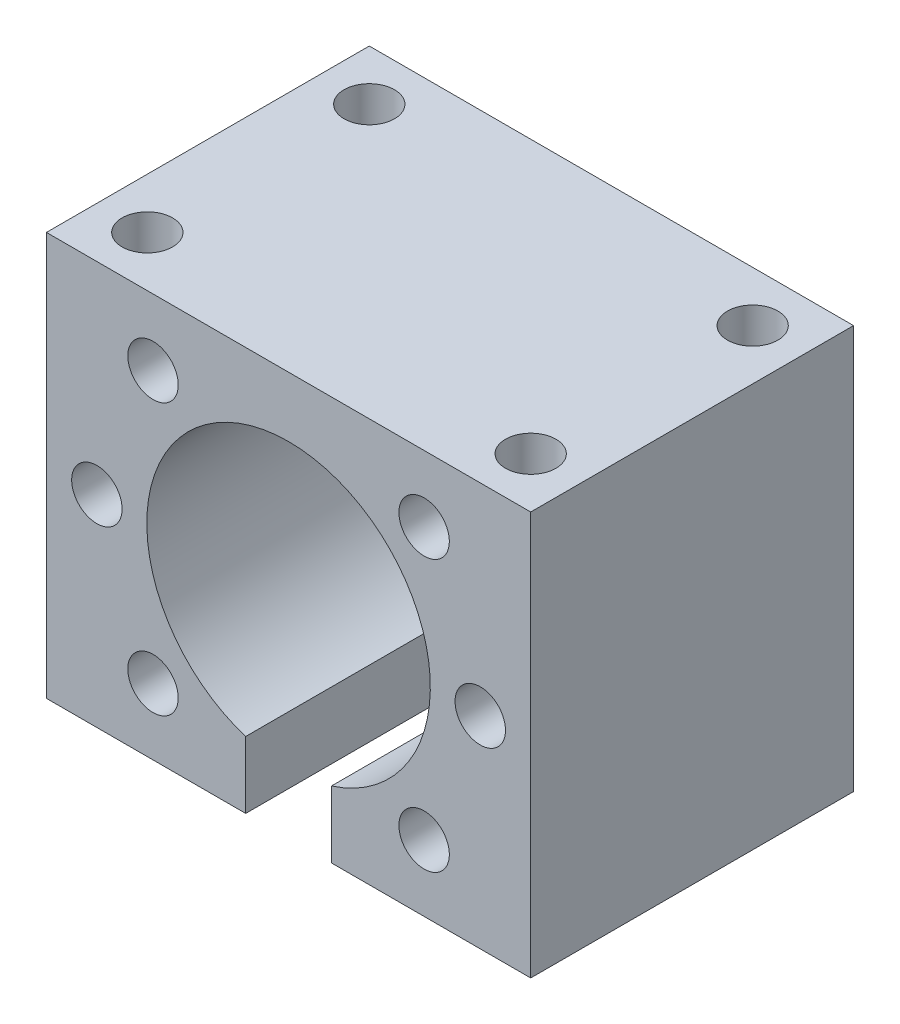
SolidWorks part; units mm, degrees
ref_plane "Front Plane" through (0, 0, 0) normal (0, 0, 1) x (1, 0, 0)
ref_plane "Top Plane" through (0, 0, 0) normal (0, 1, 0) x (1, 0, 0)
ref_plane "Right Plane" through (0, 0, 0) normal (1, 0, 0) x (0, 0, -1)
sketch "Sketch1" plane through (0, 0, 0) normal (0, 0, 1) x (1, 0, 0)
  line L0 (0, 0) -> (0, 43.8498) construction
  line L1 (-24, 40) -> (-24, 0)
  line L2 (-24, 0) -> (-4.25, 0)
  line L3 (-24, 40) -> (24, 40)
  line L4 (0, 20) -> (-28.6191, 20) construction
  line L5 (-4.25, 0) -> (-4.25, 6.6082)
  line L6 (4.25, 0) -> (4.25, 6.6082)
  line L7 (24, 0) -> (4.25, 0)
  line L8 (24, 40) -> (24, 0)
  arc A0 (4.25, 6.6082) -> (-4.25, 6.6082) centre (0, 20) ccw
  point P12 (0, 40)
  dimension "D1" = 28.1
  dimension "D2" = 20
  dimension "D3" = 24
  dimension "D4" = 8.5
  dimension "D5" = 40
extrude "Boss-Extrude1" add sketch "Sketch1" along normal blind 32
sketch "Sketch2" plane through (0, 0, 32) normal (0, 0, 1) x (1, 0, 0)
  line L0 (0, 20) -> (-26.3462, 20) construction
  line L1 (0, 20) -> (0, 43.9567) construction
  line L2 (-13.435, 33.435) -> (0, 20) construction
  circle A0 centre (0, 20) radius 19 construction
  circle A1 centre (-19, 20) radius 2.5
  circle A2 centre (-13.435, 33.435) radius 2.5
  circle A5 centre (-13.435, 6.565) radius 2.5
  circle A6 centre (13.435, 33.435) radius 2.5
  circle A7 centre (19, 20) radius 2.5
  circle A8 centre (13.435, 6.565) radius 2.5
  dimension "D1" = 38
  dimension "D2" = 5
  dimension "D3" = 45
hole_wizard "Tap Drill for M5 Tap1" positions "3DSketch1" profile "Sketch3" hole size "M5" standard "GB"
sketch3d "3DSketch1"
  point P0 (-13.435, 33.435, 32)
  point P3 (-19, 20, 32)
  point P6 (-13.435, 6.565, 32)
  point P9 (13.435, 6.565, 32)
  point P12 (19, 20, 32)
  point P15 (13.435, 33.435, 32)
sketch "Sketch3" plane through (-13.435, 33.435, 32) normal (1, 0, 0) x (0, -1, 0)
  line L0 (0, 0) -> (0, 21.5022)
  line L1 (0, 21.5022) -> (2.5, 20)
  line L2 (2.5, 20) -> (2.5, 0)
  line L5 (2.5, 0) -> (0, 0)
  line L10 (0, 21.5022) -> (-2.5, 20) construction
  line L11 (0, -6.35) -> (0, 107.95) construction
  dimension "Hole Dia." = 5
  dimension "Hole Depth" = 20
  dimension "Drill Angle" = 118
sketch "Sketch4" plane through (0, 40, 0) normal (0, 1, 0) x (1, 0, 0)
  line L0 (0, 0) -> (0, -36.5542) construction
  line L1 (-24, -16) -> (0, -16) construction
  line L2 (-24, -32) -> (-24, 0) construction
  circle A0 centre (-19, -5) radius 2.846
  circle A1 centre (-19, -27) radius 2.846
  circle A2 centre (19, -27) radius 2.846
  circle A3 centre (19, -5) radius 2.846
  dimension "D1" = 19
  dimension "D2" = 11
hole_wizard "Tap Drill for M5 Tap2" positions "3DSketch2" profile "Sketch5" hole size "M5" standard "GB"
sketch3d "3DSketch2"
  point P0 (-19, 40, 5)
  point P3 (-19, 40, 27)
  point P6 (19, 40, 27)
  point P9 (19, 40, 5)
sketch "Sketch5" plane through (-19, 40, 5) normal (1, 0, 0) x (0, 0, 1)
  line L0 (0, 0) -> (0, 21.5022)
  line L1 (0, 21.5022) -> (2.5, 20)
  line L2 (2.5, 20) -> (2.5, 0)
  line L5 (2.5, 0) -> (0, 0)
  line L10 (0, 21.5022) -> (-2.5, 20) construction
  line L11 (0, -6.35) -> (0, 107.95) construction
  dimension "Hole Dia." = 5
  dimension "Hole Depth" = 20
  dimension "Drill Angle" = 118
